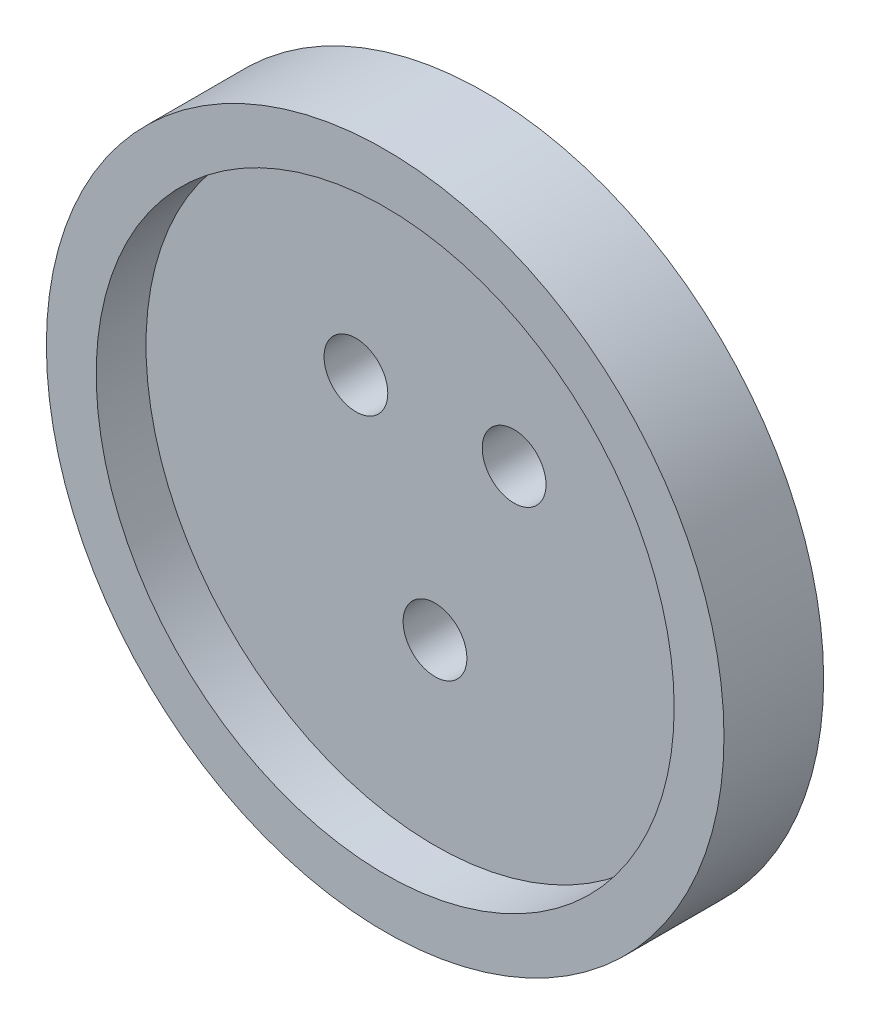
SolidWorks part; units mm, degrees
ref_plane "Front" through (0, 0, 0) normal (0, 0, 1) x (1, 0, 0)
ref_plane "Top" through (0, 0, 0) normal (0, 1, 0) x (1, 0, 0)
ref_plane "Right" through (0, 0, 0) normal (1, 0, 0) x (0, 0, -1)
sketch "Sketch1" plane through (0, 0, 0) normal (0, 0, 1) x (1, 0, 0)
  circle A0 centre (0, 0) radius 24
extrude "Extrude1" add sketch "Sketch1" along normal blind 4
sketch "Sketch2" plane through (0, 0, 4) normal (0, 0, 1) x (1, 0, 0)
  circle A0 centre (0, 0) radius 2.5 construction
  circle A2 centre (0, 0) radius 24
extrude "Extrude2" add sketch "Sketch2" along normal blind 1
sketch "Sketch3" plane through (0, 0, 5) normal (0, 0, 1) x (1, 0, 0)
  circle A1 centre (-7.9375, 7.9375) radius 3.2
  circle A2 centre (7.9375, 7.9375) radius 3.2
  circle A3 centre (0, -11.1125) radius 3.2
extrude "Extrude3" cut sketch "Sketch3" against normal through all
sketch "Sketch4" plane through (0, 0, 0) normal (0, 0, -1) x (-1, 0, 0)
  circle A0 centre (0, 0) radius 24
  circle A1 centre (0, 0) radius 34
extrude "Extrude4" add sketch "Sketch4" against normal blind 5
sketch "Sketch5" plane through (0, 0, 5) normal (0, 0, 1) x (1, 0, 0)
  circle A0 centre (0, 0) radius 34
  circle A1 centre (0, 0) radius 29
extrude "Extrude5" add sketch "Sketch5" along normal blind 5
